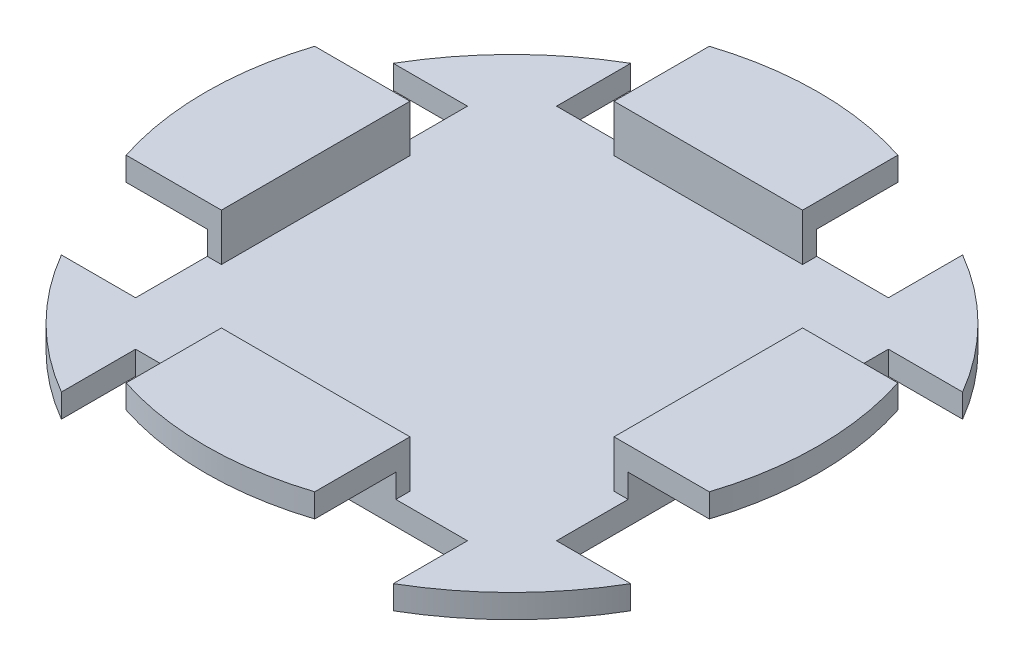
SolidWorks part; units mm, degrees
material "6061 Alloy"
ref_plane "Front Plane" through (0, 0, 0) normal (0, 0, 1) x (1, 0, 0)
ref_plane "Top Plane" through (0, 0, 0) normal (0, 1, 0) x (1, 0, 0)
ref_plane "Right Plane" through (0, 0, 0) normal (1, 0, 0) x (0, 0, -1)
sketch "Sketch1" plane through (0, 0, 0) normal (0, 1, 0) x (1, 0, 0)
  circle A0 centre (0, 0) radius 88.773
  dimension "D1" = 177.546
extrude "Base" add sketch "Sketch1" along normal blind 6.35
sketch "Sketch2" plane through (0, 6.35, 0) normal (0, 1, 0) x (1, 0, 0)
  line L3 (0, 0) -> (0, -82.55) construction
  line L4 (-25.4, -78.5452) -> (-25.4, -52.8912)
  line L5 (-25.4, -52.8912) -> (0, -52.8912)
  line L6 (0, -52.8912) -> (25.4, -52.8912)
  line L7 (25.4, -52.8912) -> (25.4, -78.5452)
  arc A1 (25.4, -78.5452) -> (0, -82.55) centre (0, 0) cw
  arc A4 (-25.4, -78.5452) -> (0, -82.55) centre (0, 0) ccw
  circle A5 centre (0, 0) radius 88.773 construction
  dimension "D3" = 82.55
  dimension "D1" = 25.4
  dimension "D2" = 25.654
extrude "Stopper" add sketch "Sketch2" along normal blind 12.7
sketch "Sketch5" plane through (0, 19.05, 0) normal (0, 1, 0) x (1, 0, 0)
  line L3 (0, 0) -> (0, -88.773) construction
  line L4 (-44.704, -76.6955) -> (-44.704, -56.7012)
  line L5 (-44.704, -56.7012) -> (0, -56.7012)
  line L6 (0, -56.7012) -> (44.704, -56.7012)
  line L7 (44.704, -56.7012) -> (44.704, -76.6955)
  line L8 (25.4, -78.5452) -> (25.4, -52.8912) construction
  line L9 (25.4, -52.8912) -> (-25.4, -52.8912) construction
  arc A1 (44.704, -76.6955) -> (0, -88.773) centre (0, 0) cw
  arc A4 (-44.704, -76.6955) -> (0, -88.773) centre (0, 0) ccw
  circle A7 centre (0, 0) radius 88.773 construction
  dimension "D1" = 3.81
  dimension "D2" = 19.304
extrude "Stopper Gap" cut sketch "Sketch5" along direction (0, -1, 0) on the side against the normal through all from offset 6.35 offset against normal yes
pattern_circular "CirPattern1" count 4 every 90 about axis through (0, 0, 0) along (0, 1, 0) of "Stopper Gap", "Stopper"
